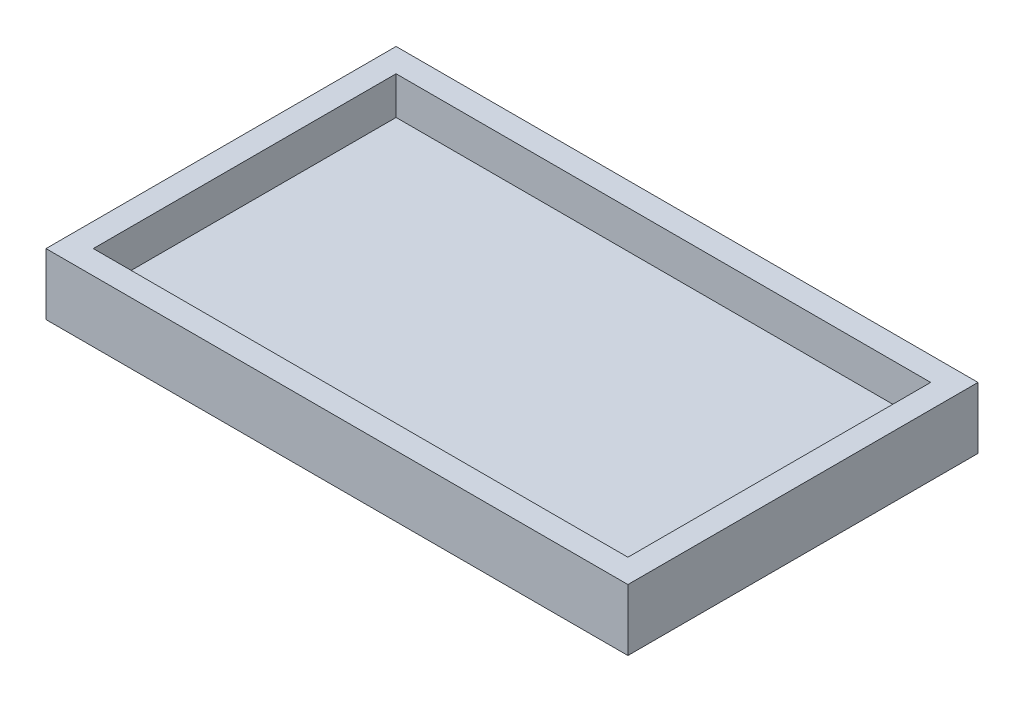
SolidWorks part; units mm, degrees
ref_plane "Front Plane" through (0, 0, 0) normal (0, 0, 1) x (1, 0, 0)
ref_plane "Top Plane" through (0, 0, 0) normal (0, 1, 0) x (1, 0, 0)
ref_plane "Right Plane" through (0, 0, 0) normal (1, 0, 0) x (0, 0, -1)
sketch "Sketch1" plane through (0, 0, 0) normal (0, 1, 0) x (1, 0, 0)
  line L1 (61.5, 37) -> (-61.5, 37)
  line L2 (61.5, 37) -> (61.5, -37)
  line L3 (61.5, -37) -> (-61.5, -37)
  line L4 (-61.5, 37) -> (-61.5, -37)
  line L5 (61.5, 37) -> (-61.5, -37) construction
  line L6 (61.5, -37) -> (-61.5, 37) construction
  point P0 (0, 0)
extrude "Boss-Extrude1" add sketch "Sketch1" along normal blind 13
sketch "Sketch3" plane through (0, 13, 0) normal (0, 1, 0) x (1, 0, 0)
  line L1 (-56.5, 32) -> (56.5, 32)
  line L2 (-56.5, 32) -> (-56.5, -32)
  line L3 (-56.5, -32) -> (56.5, -32)
  line L4 (56.5, 32) -> (56.5, -32)
  line L5 (-56.5, 32) -> (56.5, -32) construction
  line L6 (-56.5, -32) -> (56.5, 32) construction
  point P0 (0, 0)
extrude "Cut-Extrude1" cut sketch "Sketch3" against normal blind 8
